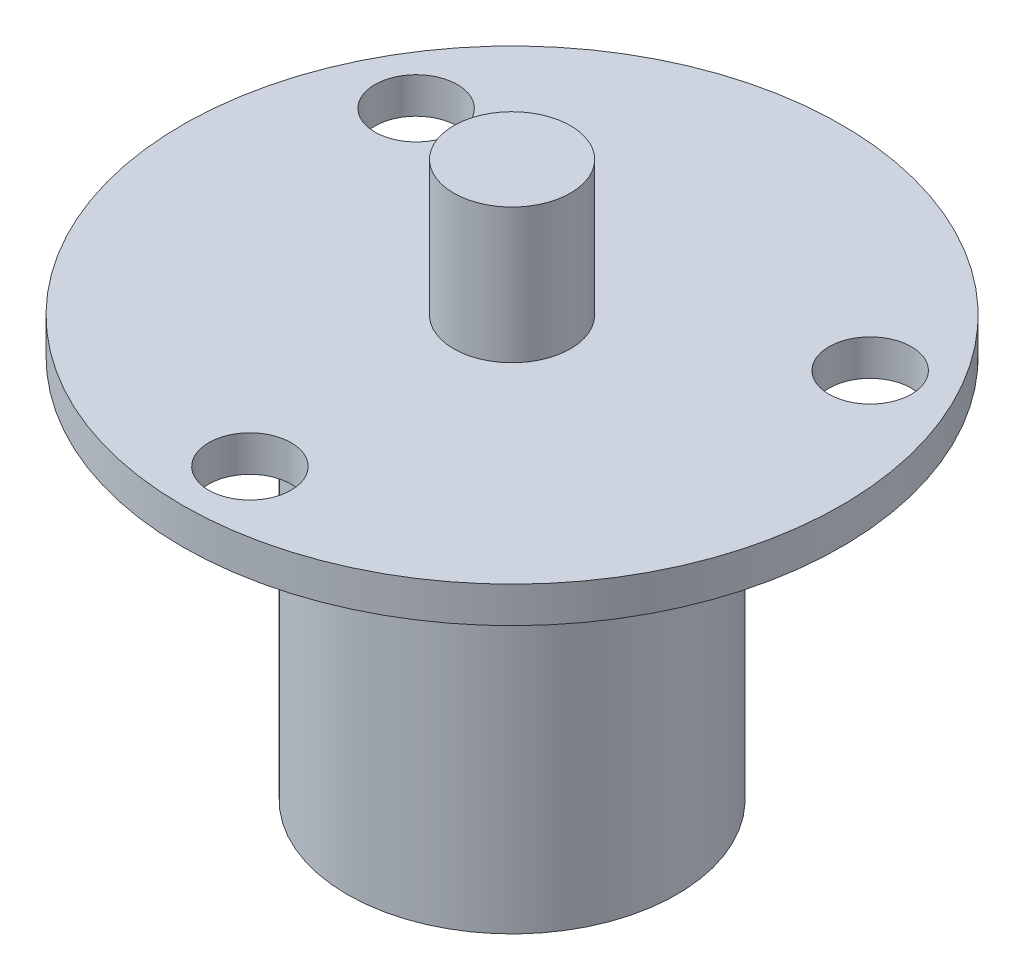
SolidWorks part; units mm, degrees
ref_plane "Front Plane" through (0, 0, 0) normal (0, 0, 1) x (1, 0, 0)
ref_plane "Top Plane" through (0, 0, 0) normal (0, 1, 0) x (1, 0, 0)
ref_plane "Right Plane" through (0, 0, 0) normal (1, 0, 0) x (0, 0, -1)
sketch "Sketch1" plane through (0, 0, 0) normal (0, 1, 0) x (1, 0, 0)
  line L0 (0, -17.5) -> (-15.1554, 8.75) construction
  line L1 (-15.1554, 8.75) -> (15.1554, 8.75) construction
  line L2 (15.1554, 8.75) -> (0, -17.5) construction
  circle A0 centre (0, 0) radius 22
  circle A1 centre (-15.1554, 8.75) radius 2.75
  circle A2 centre (0, 0) radius 17.5 construction
  circle A3 centre (15.1554, 8.75) radius 2.75
  circle A4 centre (0, -17.5) radius 2.75
  dimension "D1" = 44
  dimension "D2" = 5.5
  dimension "D3" = 35
extrude "Boss-Extrude1" add sketch "Sketch1" along normal blind 2.4
sketch "Sketch2" plane through (0, 0, 0) normal (0, -1, 0) x (1, 0, 0)
  circle A0 centre (0, 0) radius 11
  dimension "D1" = 22
extrude "Boss-Extrude2" add sketch "Sketch2" along normal blind 25.6
sketch "Sketch3" plane through (0, 2.4, 0) normal (0, 1, 0) x (1, 0, 0)
  circle A0 centre (0, 0) radius 3.9
  dimension "D1" = 7.8
extrude "Boss-Extrude3" add sketch "Sketch3" along normal blind 9
